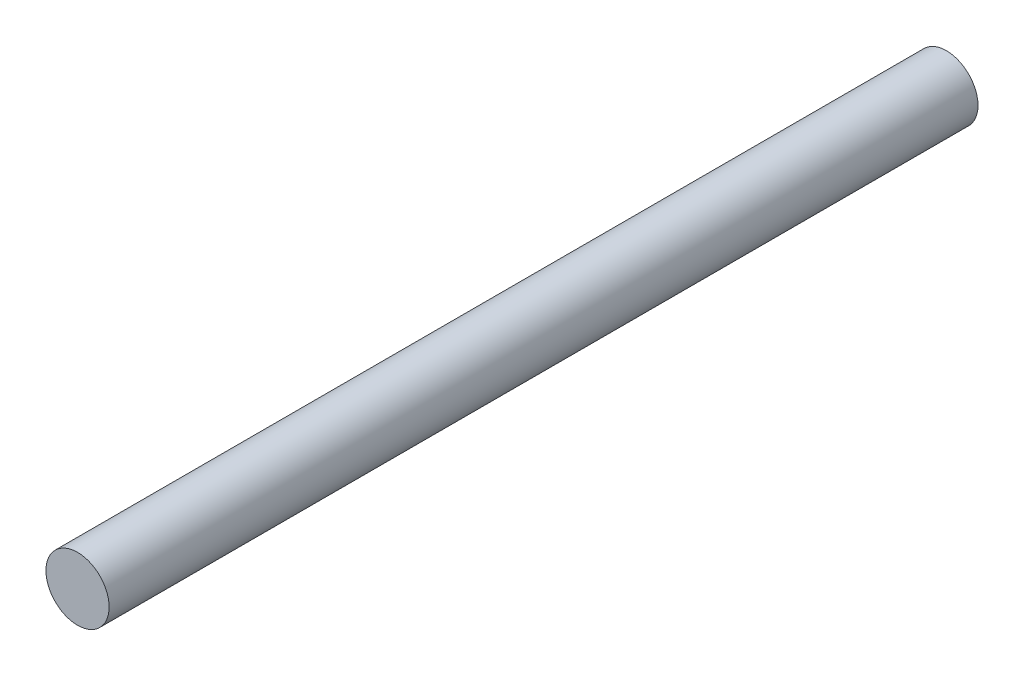
SolidWorks part; units mm, degrees
ref_plane "Alzado" through (0, 0, 0) normal (0, 0, 1) x (1, 0, 0)
ref_plane "Planta" through (0, 0, 0) normal (0, 1, 0) x (1, 0, 0)
ref_plane "Vista lateral" through (0, 0, 0) normal (1, 0, 0) x (0, 0, -1)
sketch "Croquis1" plane through (0, 0, 0) normal (0, 0, 1) x (1, 0, 0)
  circle A0 centre (0, 0) radius 4
  dimension "D1" = 8
extrude "Saliente-Extruir1" add sketch "Croquis1" along normal blind 110
